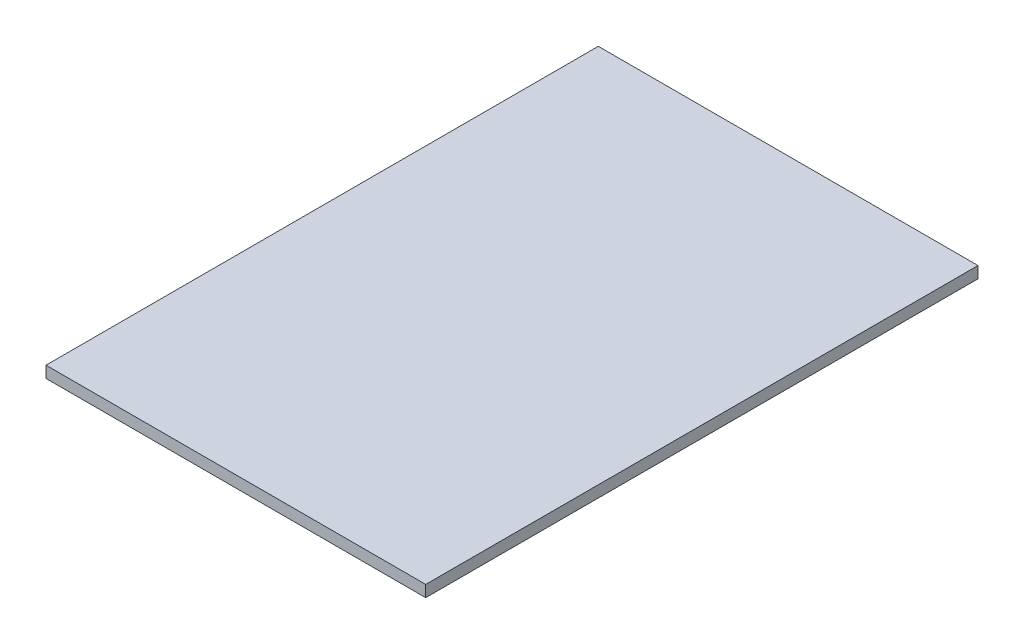
SolidWorks part; units mm, degrees
ref_plane "Front Plane" through (0, 0, 0) normal (0, 0, 1) x (1, 0, 0)
ref_plane "Top Plane" through (0, 0, 0) normal (0, 1, 0) x (1, 0, 0)
ref_plane "Right Plane" through (0, 0, 0) normal (1, 0, 0) x (0, 0, -1)
sketch "Sketch2" plane through (0, 0, 0) normal (0, 1, 0) x (1, 0, 0)
  line L1 (-33, 48) -> (33, 48)
  line L2 (-33, 48) -> (-33, -48)
  line L3 (-33, -48) -> (33, -48)
  line L4 (33, 48) -> (33, -48)
  line L5 (-33, 48) -> (33, -48) construction
  line L6 (-33, -48) -> (33, 48) construction
  point P0 (0, 0)
  dimension "D1" = 96
  dimension "D2" = 66
extrude "Boss-Extrude1" add sketch "Sketch2" along normal blind 2 contours L2 L3 L4 L1
